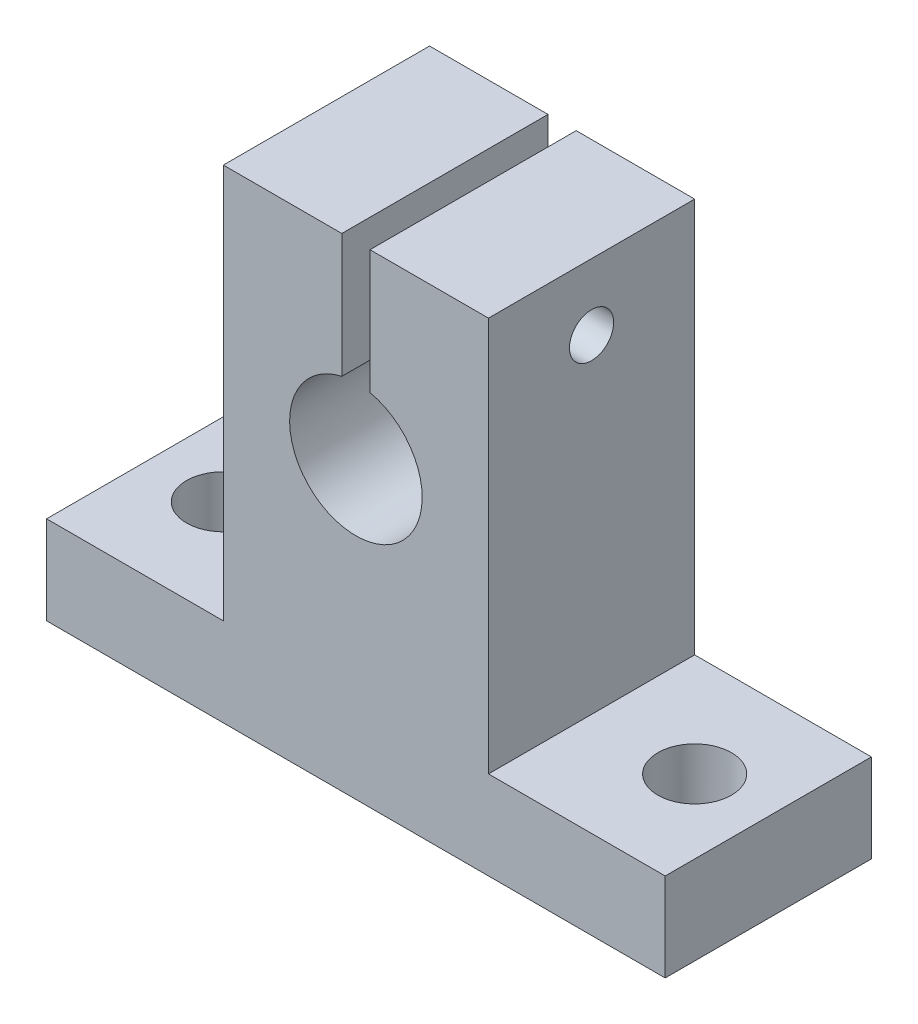
SolidWorks part; units mm, degrees
ref_plane "Front" through (0, 0, 0) normal (0, 0, 1) x (1, 0, 0)
ref_plane "Top" through (0, 0, 0) normal (0, 1, 0) x (1, 0, 0)
ref_plane "Right" through (0, 0, 0) normal (1, 0, 0) x (0, 0, -1)
sketch "Sketch1" plane through (0, 0, 0) normal (0, 0, 1) x (1, 0, 0)
  line L0 (-0.9563, 29.8) -> (-0.9563, 21.3972)
  line L1 (-21, 3) -> (-9, 3)
  line L2 (-21, 3) -> (-21, -3)
  line L3 (-21, -3) -> (21, -3)
  line L4 (21, 3) -> (21, -3)
  line L5 (-21, 3) -> (21, -3) construction
  line L6 (-21, -3) -> (21, 3) construction
  line L7 (-9, 29.8) -> (-0.9563, 29.8)
  line L8 (-9, 29.8) -> (-9, 3)
  line L10 (9, 29.8) -> (9, 3)
  line L11 (0, 30.914) -> (0, 9.6226) construction
  line L12 (0.9563, 29.8) -> (0.9563, 21.3972)
  line L13 (0.9563, 29.8) -> (9, 29.8)
  line L14 (9, 3) -> (21, 3)
  arc A0 (-0.9563, 21.3972) -> (0.9563, 21.3972) centre (0, 17) ccw
  point P0 (0, 0)
  point P6 (0, 3)
  dimension "D5" = 12.8
  dimension "D1" = 42
  dimension "D2" = 6
  dimension "D3" = 18
  dimension "D4" = 26.8
extrude "Boss-Extrude1" add sketch "Sketch1" along normal blind 14
sketch "Sketch2" plane through (0, 3, 0) normal (0, 1, 0) x (1, 0, 0)
  line L0 (-21, -14) -> (-21, 0) construction
  line L1 (0, 3.0944) -> (0, -20.109) construction
  circle A0 centre (-16, -7) radius 2.5
  circle A1 centre (16, -7) radius 2.5
  dimension "D1" = 5
extrude "Cut-Extrude1" cut sketch "Sketch2" against normal up to next
sketch "Sketch3" plane through (-9, 0, 0) normal (-1, 0, 0) x (0, 0, 1)
  line L0 (14, 29.8) -> (0, 29.8) construction
  circle A0 centre (7, 25.3) radius 1.5
  dimension "D1" = 4.5
extrude "Cut-Extrude2" cut sketch "Sketch3" against normal through all
